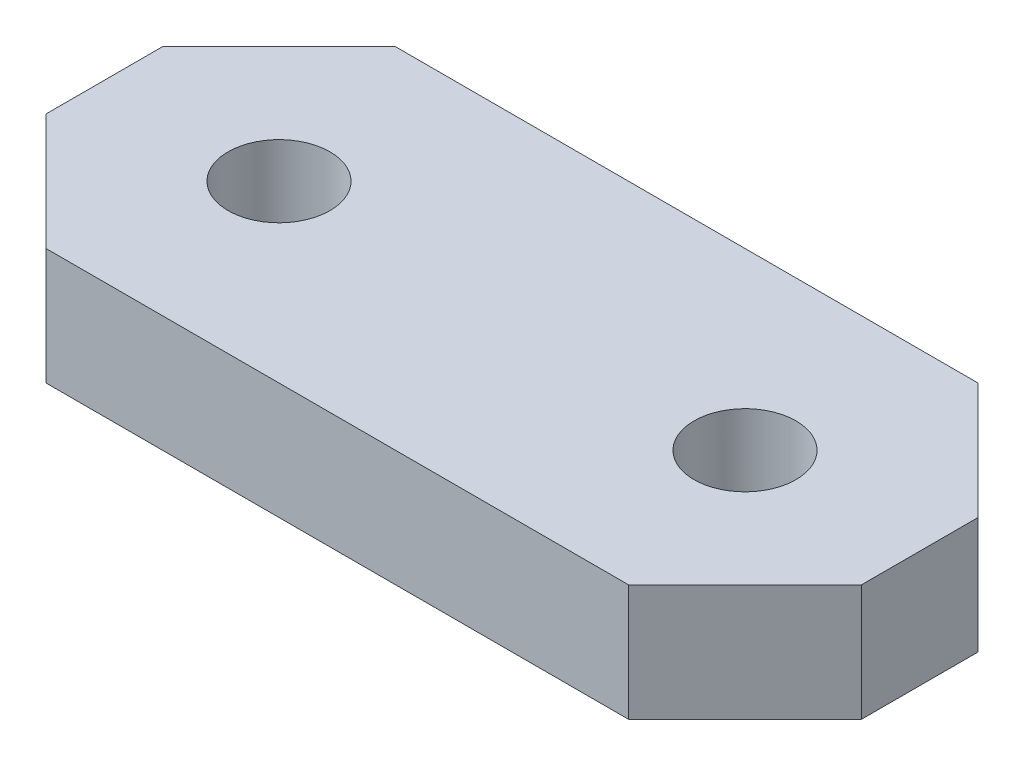
SolidWorks part; units mm, degrees
ref_plane "Front Plane" through (0, 0, 0) normal (0, 0, 1) x (1, 0, 0)
ref_plane "Top Plane" through (0, 0, 0) normal (0, 1, 0) x (1, 0, 0)
ref_plane "Right Plane" through (0, 0, 0) normal (1, 0, 0) x (0, 0, -1)
sketch "Sketch1" plane through (0, 0, 0) normal (0, 0, 1) x (1, 0, 0)
  line L0 (0, 0) -> (12, 0)
  line L8 (16, 0) -> (28, 0)
  line L9 (28, 0) -> (28, 4)
  line L10 (28, 4) -> (0, 4)
  line L11 (0, 4) -> (0, 0)
  line L12 (12, 0) -> (16, 0)
  dimension "D1" = 4
  dimension "D3" = 12
extrude "Boss-Extrude1" add sketch "Sketch1" along normal blind 12
sketch "Sketch2" plane through (0, 0, 0) normal (0, -1, 0) x (-1, 0, 0)
  line L0 (-28, -12) -> (-16, 0) construction
  line L1 (-16, 0) -> (-12, 0) construction
  line L2 (-12, 0) -> (0, -12) construction
  circle A0 centre (-6, -6) radius 1.75
  circle A1 centre (-22, -6) radius 1.75
  dimension "D1" = 3.5
extrude "Cut-Extrude1" cut sketch "Sketch2" against normal through all both and the other way through all
chamfer "Chamfer1" distance 4 angle 45 4 edges at (0, 2, 0) (0, 2, 12) (28, 2, 0) (28, 2, 12)
